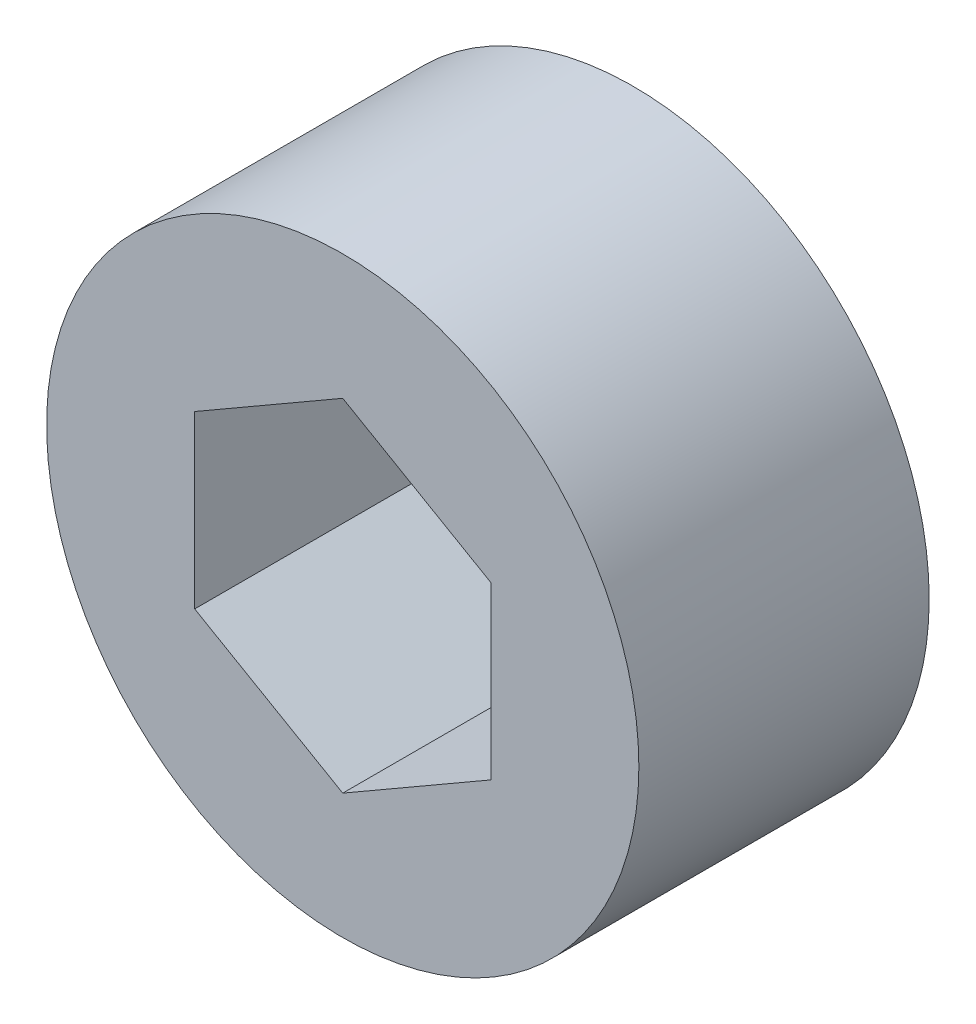
SolidWorks part; units mm, degrees
ref_plane "Front" through (0, 0, 0) normal (0, 0, 1) x (1, 0, 0)
ref_plane "Top" through (0, 0, 0) normal (0, 1, 0) x (1, 0, 0)
ref_plane "Right" through (0, 0, 0) normal (1, 0, 0) x (0, 0, -1)
sketch "Sketch1" plane through (0, 0, 0) normal (0, 0, 1) x (1, 0, 0)
  circle A0 centre (0, 0) radius 6.477
  dimension "D1" = 12.954
extrude "Boss-Extrude1" add sketch "Sketch1" along normal blind 6.35
sketch "Sketch2" plane through (0, 0, 6.35) normal (0, 0, 1) x (1, 0, 0)
  line L0 (0, 0) -> (0, 3.7395) construction
  line L1 (3.2385, 1.8697) -> (0, 3.7395)
  line L2 (0, 3.7395) -> (-3.2385, 1.8697)
  line L3 (-3.2385, 1.8697) -> (-3.2385, -1.8697)
  line L4 (-3.2385, -1.8697) -> (0, -3.7395)
  line L5 (0, -3.7395) -> (3.2385, -1.8697)
  line L6 (3.2385, -1.8697) -> (3.2385, 1.8697)
  circle A0 centre (0, 0) radius 3.2385 construction
  point P1 (-1.6192, -2.8046)
  dimension "D1" = 6.477
extrude "Cut-Extrude1" cut sketch "Sketch2" against normal through all
sketch "Sketch3" plane through (0, 0, 6.35) normal (0, 0, 1) x (1, 0, 0)
  circle A0 centre (0, 3.7395) radius 0.3175
  dimension "D1" = 0.635
extrude "Cut-Extrude2" [suppressed] cut sketch "Sketch3" against normal through all
pattern_circular "CirPattern4" [suppressed] count 6 over 360
fillet "Fillet1" [suppressed] radius 0.635
